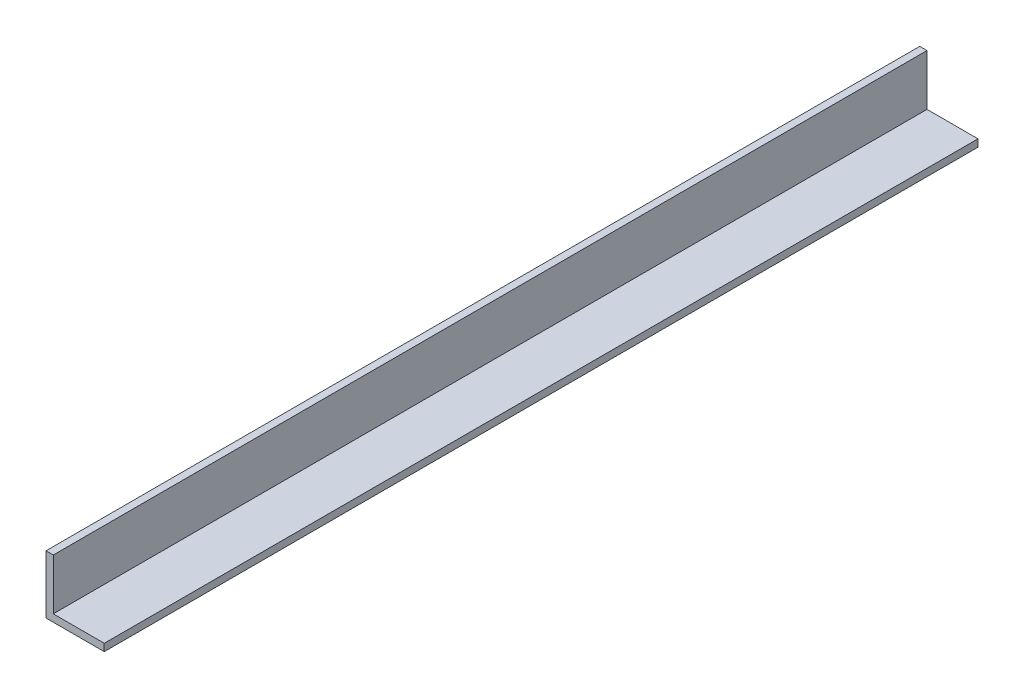
SolidWorks part; units mm, degrees
material "1060 Alloy"
ref_plane "Front Plane" through (0, 0, 0) normal (0, 0, 1) x (1, 0, 0)
ref_plane "Top Plane" through (0, 0, 0) normal (0, 1, 0) x (1, 0, 0)
ref_plane "Right Plane" through (0, 0, 0) normal (1, 0, 0) x (0, 0, -1)
sketch "Sketch1" plane through (0, 0, 0) normal (0, 0, 1) x (1, 0, 0)
  line L1 (0, 0) -> (25.4, 0)
  line L2 (0, 0) -> (0, 25.4)
  line L3 (0, 25.4) -> (3.175, 25.4)
  line L4 (25.4, 0) -> (25.4, 3.175)
  line L7 (25.4, 3.175) -> (3.175, 3.175)
  line L8 (3.175, 25.4) -> (3.175, 3.175)
  dimension "D1" = 25.4
  dimension "D2" = 3.175
extrude "Boss-Extrude1" add sketch "Sketch1" along normal blind 381
